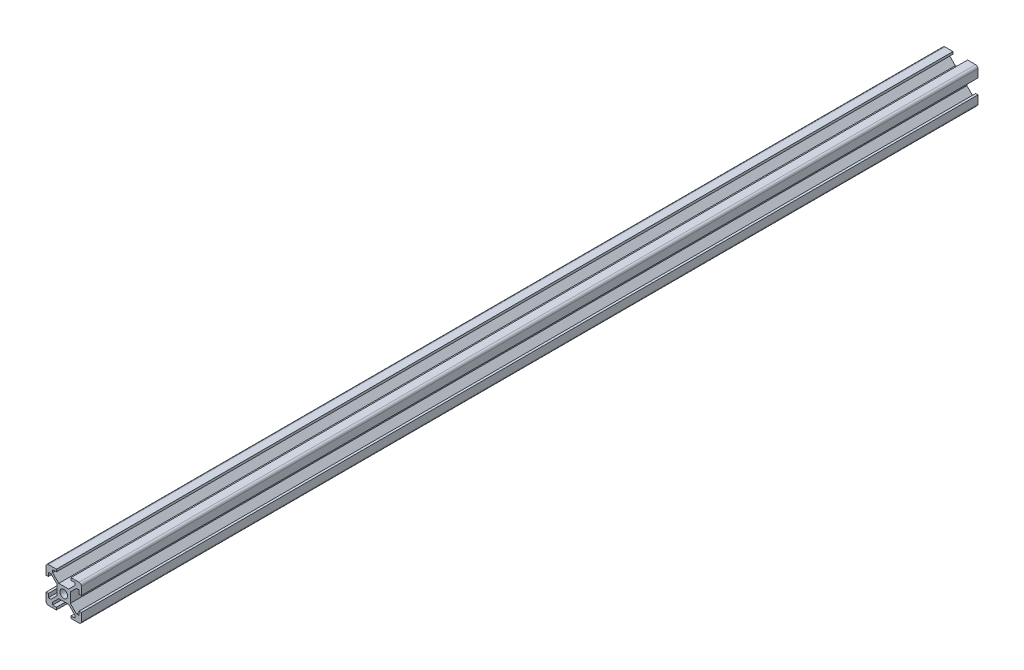
SolidWorks part; units mm, degrees
ref_plane "前视基准面" through (0, 0, 0) normal (0, 0, 1) x (1, 0, 0)
ref_plane "上视基准面" through (0, 0, 0) normal (0, 1, 0) x (1, 0, 0)
ref_plane "右视基准面" through (0, 0, 0) normal (1, 0, 0) x (0, 0, -1)
sketch "草图1" plane through (0, 0, 0) normal (0, 0, 1) x (1, 0, 0)
  line L0 (-13.1606, 0) -> (11.1587, 0) construction
  line L1 (0, 10.9428) -> (0, -12.3014) construction
  line L2 (-13.1302, 13.1302) -> (13.1302, -13.1302) construction
  line L3 (-2.0929, 2.8) -> (2.0929, 2.8)
  line L4 (-2.8, 2.0929) -> (-2.8, -2.0929)
  line L5 (-2.0929, -2.8) -> (2.0929, -2.8)
  line L6 (2.8, 2.0929) -> (2.8, -2.0929)
  line L7 (-2.0929, 2.8) -> (-4.7, 5.4071)
  line L8 (-2.8, 2.0929) -> (-5.4071, 4.7)
  line L9 (-7.5, 6.5) -> (-7.5, 3.1)
  line L10 (-7.5, 3.1) -> (-6.5, 3.1)
  line L11 (-6.5, 3.1) -> (-6.5, 4.7)
  line L12 (-6.5, 4.7) -> (-5.4071, 4.7)
  line L13 (-4.7, 6.5) -> (-4.7, 5.4071)
  line L14 (-3.1, 6.5) -> (-4.7, 6.5)
  line L15 (-3.1, 7.5) -> (-3.1, 6.5)
  line L16 (-6.5, 7.5) -> (-3.1, 7.5)
  line L17 (2.8, 2.0929) -> (5.4071, 4.7)
  line L18 (2.0929, 2.8) -> (4.7, 5.4071)
  line L19 (6.5, 7.5) -> (3.1, 7.5)
  line L20 (3.1, 7.5) -> (3.1, 6.5)
  line L21 (3.1, 6.5) -> (4.7, 6.5)
  line L22 (4.7, 6.5) -> (4.7, 5.4071)
  line L23 (6.5, 4.7) -> (5.4071, 4.7)
  line L24 (6.5, 3.1) -> (6.5, 4.7)
  line L25 (7.5, 3.1) -> (6.5, 3.1)
  line L26 (7.5, 6.5) -> (7.5, 3.1)
  line L27 (2.0929, -2.8) -> (4.7, -5.4071)
  line L28 (2.8, -2.0929) -> (5.4071, -4.7)
  line L29 (7.5, -6.5) -> (7.5, -3.1)
  line L30 (7.5, -3.1) -> (6.5, -3.1)
  line L31 (6.5, -3.1) -> (6.5, -4.7)
  line L32 (6.5, -4.7) -> (5.4071, -4.7)
  line L33 (4.7, -6.5) -> (4.7, -5.4071)
  line L34 (3.1, -6.5) -> (4.7, -6.5)
  line L35 (3.1, -7.5) -> (3.1, -6.5)
  line L36 (6.5, -7.5) -> (3.1, -7.5)
  line L37 (-2.8, -2.0929) -> (-5.4071, -4.7)
  line L38 (-2.0929, -2.8) -> (-4.7, -5.4071)
  line L39 (-6.5, -7.5) -> (-3.1, -7.5)
  line L40 (-3.1, -7.5) -> (-3.1, -6.5)
  line L41 (-3.1, -6.5) -> (-4.7, -6.5)
  line L42 (-4.7, -6.5) -> (-4.7, -5.4071)
  line L43 (-6.5, -4.7) -> (-5.4071, -4.7)
  line L44 (-6.5, -3.1) -> (-6.5, -4.7)
  line L45 (-7.5, -3.1) -> (-6.5, -3.1)
  line L46 (-7.5, -6.5) -> (-7.5, -3.1)
  circle A0 centre (0, 0) radius 1.65
  arc A1 (-7.5, 6.5) -> (-6.5, 7.5) centre (-6.5, 6.5) cw
  arc A2 (6.5, 7.5) -> (7.5, 6.5) centre (6.5, 6.5) cw
  arc A3 (7.5, -6.5) -> (6.5, -7.5) centre (6.5, -6.5) cw
  arc A4 (-6.5, -7.5) -> (-7.5, -6.5) centre (-6.5, -6.5) cw
  point P26 (-7.5, 7.5)
  point P68 (0, 0)
  dimension "D1" = 3.3
  dimension "D10" = 1
  dimension "D2" = 45
  dimension "D4" = 1
  dimension "D5" = 7.5
  dimension "D6" = 4.7
  dimension "D7" = 1
  dimension "D8" = 3.1
  dimension "D9" = 4.7
  dimension "D11" = 4
extrude "凸台-拉伸1" add sketch "草图1" along normal blind 380
cosmetic thread "装饰螺纹线1" parameters "D1"=20, "D2"=4
cosmetic thread "装饰螺纹线2" parameters "D1"=20, "D2"=4
